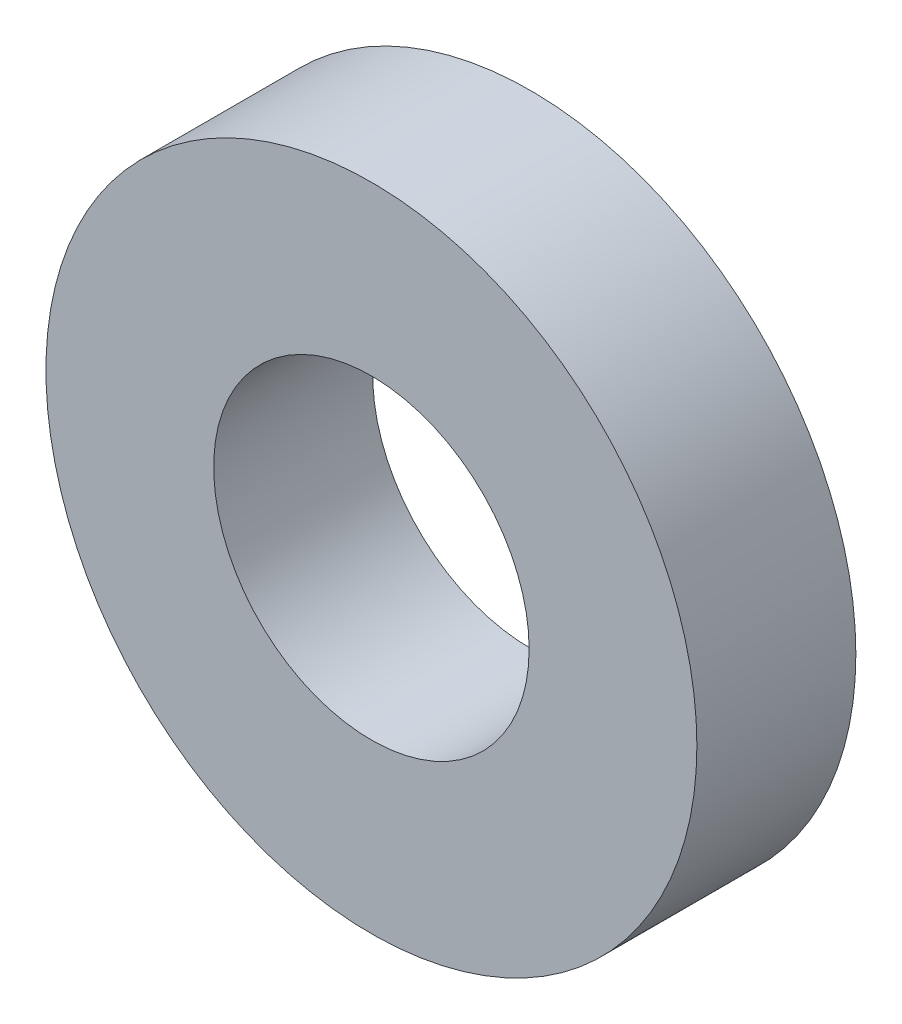
SolidWorks part; units mm, degrees
ref_plane "Front Plane" through (0, 0, 0) normal (0, 0, 1) x (1, 0, 0)
ref_plane "Top Plane" through (0, 0, 0) normal (0, 1, 0) x (1, 0, 0)
ref_plane "Right Plane" through (0, 0, 0) normal (1, 0, 0) x (0, 0, -1)
sketch "Sketch1" plane through (0, 0, 0) normal (0, 0, 1) x (1, 0, 0)
  circle A0 centre (0, 0) radius 6.5
  circle A1 centre (0, 0) radius 3.15
  dimension "OD" = 13
  dimension "ID" = 6.3
extrude "Extrude1" add sketch "Sketch1" along normal mid plane 3.175
sketch "Sketch2" plane through (0, 0, 0) normal (1, 0, 0) x (0, 0, -1)
  line L0 (-1.5875, -3.15) -> (1.5875, -3.15) construction
  line L2 (1.5875, 3.15) -> (1.5875, -3.15) construction
  line L3 (1.5875, 3.15) -> (-1.5875, 3.15) construction
  line L5 (-1.5875, -3.15) -> (1.5875, -3.15)
  line L6 (1.5875, 3.15) -> (-1.5875, 3.15)
  dimension "D1" = 3.175
sketch "Sketch4" plane through (0, 0, 1.5875) normal (0, 0, 1) x (1, 0, 0)
  line L0 (0, 0) -> (-2.2274, 2.2274)
  line L1 (0, -55) -> (0, 55) construction
  circle A0 centre (0, 0) radius 3.15 construction
  dimension "D1" = 45
